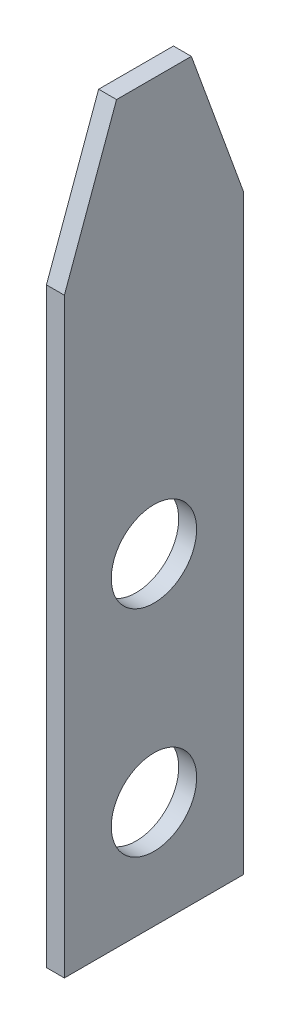
SolidWorks part; units mm, degrees
material "AISI 316 Нержавеющая сталь, лист (SS)"
ref_plane "Спереди" through (0, 0, 0) normal (0, 0, 1) x (1, 0, 0)
ref_plane "Сверху" through (0, 0, 0) normal (0, 1, 0) x (1, 0, 0)
ref_plane "Справа" through (0, 0, 0) normal (1, 0, 0) x (0, 0, -1)
sketch "Эскиз1" plane through (0, 0, 0) normal (1, 0, 0) x (0, 0, -1)
  line L1 (0, 0) -> (5, 0)
  line L2 (0, 0) -> (0, 20.5)
  line L3 (0, 20.5) -> (5, 20.5)
  line L4 (5, 0) -> (5, 20.5)
  dimension "D1" = 5
  dimension "D2" = 20.5
extrude "Бобышка-Вытянуть1" add sketch "Эскиз1" along normal blind 0.5
hole_wizard "Сверло под метчик  спиральное #21" positions "Эскиз3" profile "Эскиз2" hole size "#2-56" standard "Ansi (в дюймах)" end condition through all
sketch "Эскиз3" plane through (0, 0, 0) normal (-1, 0, 0) x (0, 0, 1)
  line L0 (0, 20.5) -> (0, 0) construction
  line L1 (0, 0) -> (-5, 0) construction
  point P0 (-2.5, 3)
  point P1 (-2.5, 9)
  dimension "D1" = 6
  dimension "D2" = 2.5
  dimension "D3" = 3
sketch "Эскиз2" plane through (0, 3, -2.5) normal (0, 1, 0) x (0, 0, 1)
  line L0 (0, 0) -> (0, 0.5)
  line L1 (0, 0.5) -> (1.1913, 0.5)
  line L2 (1.1913, 0.5) -> (1.1913, 0)
  line L5 (1.1913, 0) -> (0, 0)
  line L11 (0, -6.35) -> (0, 107.95) construction
  dimension "Диаметр сквозного отверстия" = 2.3825
  dimension "Глубина сквозного отверстия" = 0.5
chamfer "Фаска1" distance 4 angle 20 2 edges at (0.25, 20.5, -5) (0.25, 20.5, 0)
